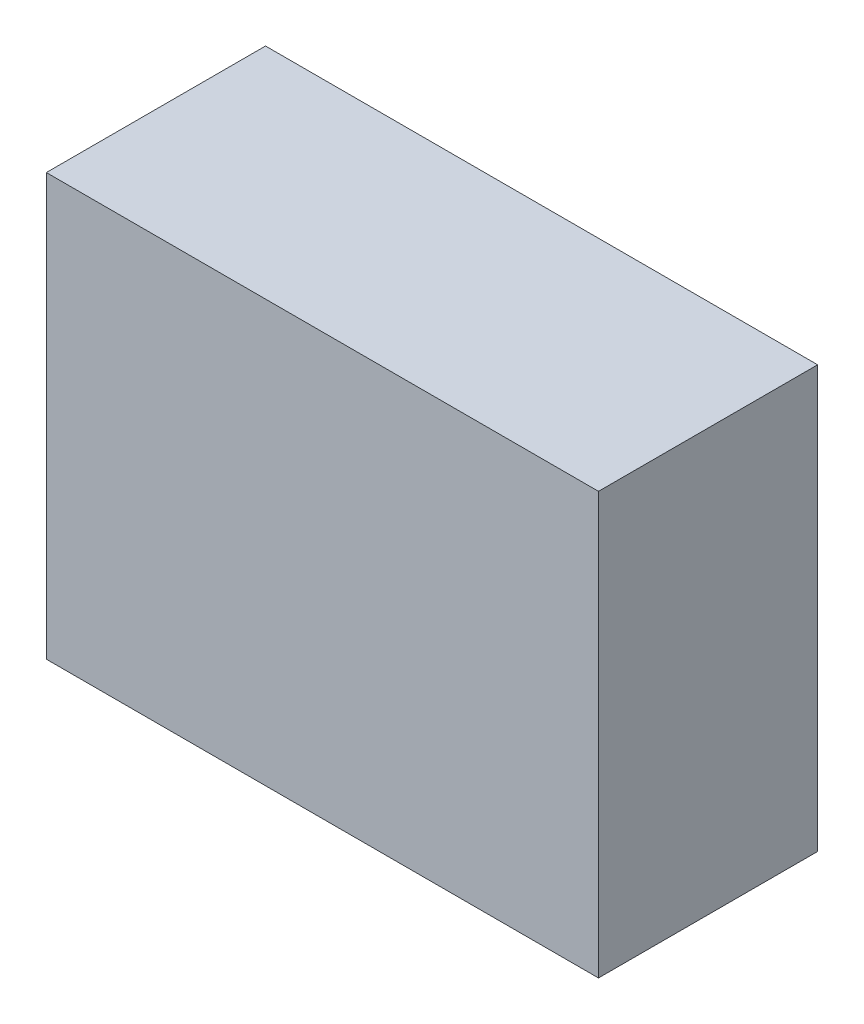
SolidWorks part; units mm, degrees
ref_plane "Front Plane" through (0, 0, 0) normal (0, 0, 1) x (1, 0, 0)
ref_plane "Top Plane" through (0, 0, 0) normal (0, 1, 0) x (1, 0, 0)
ref_plane "Right Plane" through (0, 0, 0) normal (1, 0, 0) x (0, 0, -1)
sketch "Sketch1" plane through (0, 0, 0) normal (0, 0, 1) x (1, 0, 0)
  line L1 (65.5, 50) -> (-65.5, 50)
  line L2 (65.5, 50) -> (65.5, -50)
  line L3 (65.5, -50) -> (-65.5, -50)
  line L4 (-65.5, 50) -> (-65.5, -50)
  line L5 (65.5, 50) -> (-65.5, -50) construction
  line L6 (65.5, -50) -> (-65.5, 50) construction
  point P0 (0, 0)
  dimension "D1" = 131
  dimension "D2" = 100
extrude "Boss-Extrude1" add sketch "Sketch1" along normal blind 52
